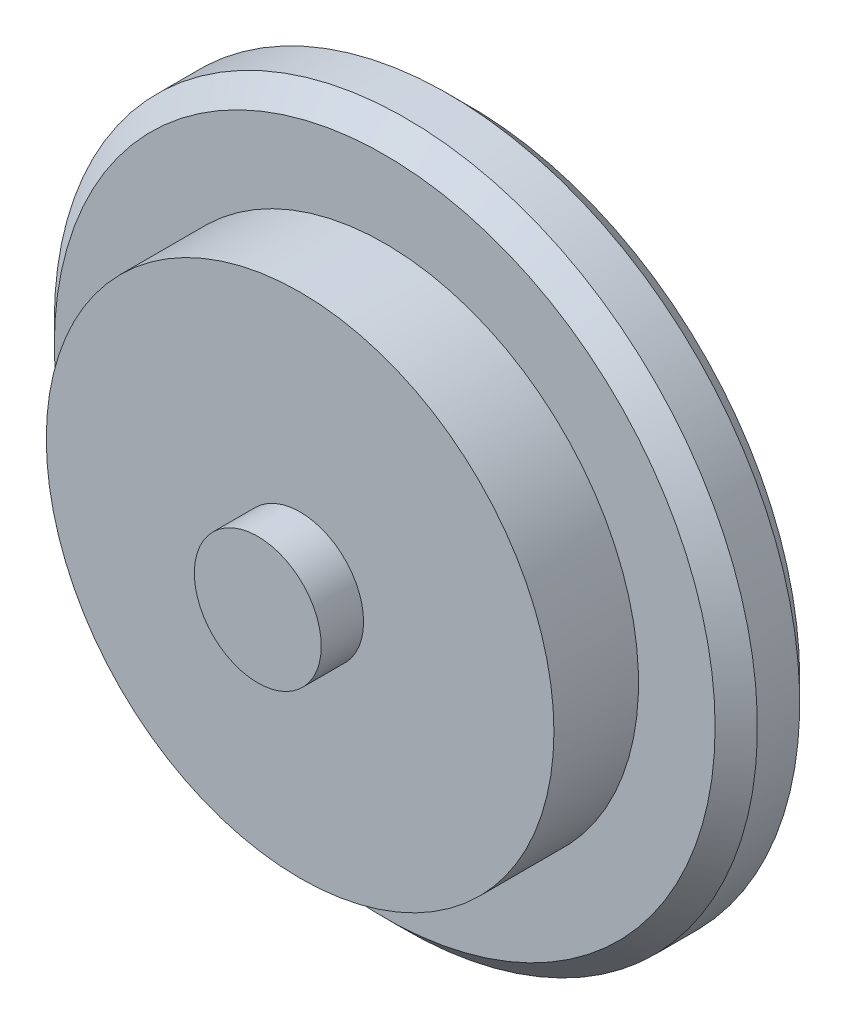
SolidWorks part; units mm, degrees
ref_plane "Front Plane" through (0, 0, 0) normal (0, 0, 1) x (1, 0, 0)
ref_plane "Top Plane" through (0, 0, 0) normal (0, 1, 0) x (1, 0, 0)
ref_plane "Right Plane" through (0, 0, 0) normal (1, 0, 0) x (0, 0, -1)
sketch "Sketch1" plane through (0, 0, 0) normal (0, 0, 1) x (1, 0, 0)
  circle A0 centre (0, 0) radius 76.2
extrude "Boss-Extrude1" add sketch "Sketch1" along normal blind 25.4
sketch "Sketch2" plane through (0, 0, 25.4) normal (0, 0, 1) x (1, 0, 0)
  circle A0 centre (0, 0) radius 19.05
extrude "Boss-Extrude2" add sketch "Sketch2" along normal blind 12.7
sketch "Sketch3" plane through (0, 0, 0) normal (0, 0, -1) x (-1, 0, 0)
  circle A0 centre (0, 0) radius 105.5417
extrude "Boss-Extrude4" add sketch "Sketch3" along normal blind 25.4
chamfer "Chamfer1" distance 6.35 angle 45 2 edges at (-105.5417, 0, -25.4) (-105.5417, 0, 0)
shell "Shell1" thickness 0.635
